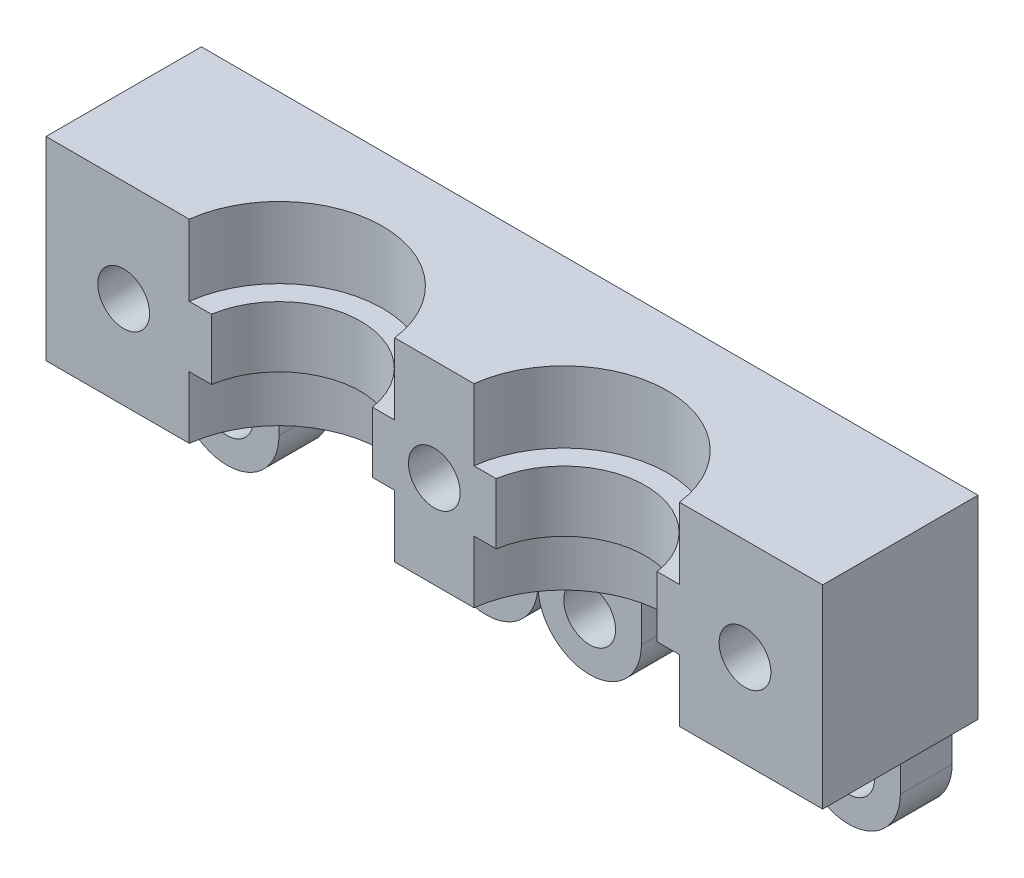
SolidWorks part; units mm, degrees
ref_plane "Piano frontale" through (0, 0, 0) normal (0, 0, 1) x (1, 0, 0)
ref_plane "Piano superiore" through (0, 0, 0) normal (0, 1, 0) x (1, 0, 0)
ref_plane "Piano destro" through (0, 0, 0) normal (1, 0, 0) x (0, 0, -1)
sketch "Schizzo1" plane through (0, 0, 0) normal (0, 0, 1) x (1, 0, 0)
  line L1 (-30, 15) -> (30, 15)
  line L2 (-30, 15) -> (-30, -15)
  line L3 (-30, -15) -> (30, -15)
  line L4 (30, 15) -> (30, -15)
  line L5 (-30, 15) -> (30, -15) construction
  line L6 (-30, -15) -> (30, 15) construction
  point P0 (0, 0)
  dimension "D1" = 60
  dimension "D2" = 30
extrude "Estrusione-Estrusione1" add sketch "Schizzo1" along normal blind 5
sketch "Schizzo2" plane through (0, 0, 5) normal (0, 0, 1) x (1, 0, 0)
  line L0 (-32.3459, -15) -> (49.5432, -15) construction
  line L1 (-32.3459, -8) -> (49.5432, -8) construction
  line L3 (30, -15) -> (30, 15) construction
  line L4 (-30, 15) -> (30, 15)
  line L5 (-30, 15) -> (-30, 7)
  line L6 (-30, 7) -> (30, 7)
  line L7 (30, 15) -> (30, 7)
  dimension "D1" = 7
extrude "Estrusione-Estrusione2" add sketch "Schizzo2" along normal blind 20
sketch "Schizzo3" plane through (0, 15, 0) normal (0, 1, 0) x (1, 0, 0)
  line L0 (0, 7.3603) -> (0, -33.3603) construction
  line L1 (11, 7.3603) -> (11, -33.3603) construction
  line L2 (30, 0) -> (-30, 0) construction
  circle A0 centre (11, -13) radius 5
  circle A1 centre (-11, -13) radius 5
  dimension "D2" = 10
  dimension "D3" = 13
  dimension "D1" = 11
extrude "Taglio-Estrusione1" cut sketch "Schizzo3" against normal up to surface (8 mm away) up to face at (-7.5, 7, 20)
fillet "Raccordo1" radius 20 2 edges at (30, 11, 25) (-30, 11, 25)
sketch "Schizzo4" plane through (0, 0, 5) normal (0, 0, 1) x (1, 0, 0)
  line L0 (-30, 7) -> (30, 7) construction
  line L1 (-30, 7) -> (30, 7)
  line L2 (-30, -8) -> (30, -8)
  line L3 (-30, -8) -> (-30, 7)
  line L4 (30, -8) -> (30, 7)
  dimension "D1" = 15
extrude "Estrusione-Estrusione3" add sketch "Schizzo4" along normal blind 10
sketch "Schizzo6" plane through (0, -8, 0) normal (0, -1, 0) x (1, 0, 0)
  line L0 (0, 28.7661) -> (0, -12.0233) construction
  line L1 (0, -7.3603) -> (0, 33.3603) construction
  circle A0 centre (-11, 13) radius 8
  circle A1 centre (11, 13) radius 8
  dimension "D1" = 16
extrude "Taglio-Estrusione2" cut sketch "Schizzo6" against normal blind 15
ref_plane "Piano1" through (-30, 7, 15) normal (0, -1, 0) x (-1, 0, 0)
sketch "Schizzo8" plane through (0, 0, 15) normal (0, 0, 1) x (1, 0, 0)
  line L1 (-30, 1.5) -> (-30, -3.2)
  line L3 (30, 1.5) -> (30, -3.2)
  line L4 (-30, 1.5) -> (30, 1.5)
  line L5 (-30, -3.2) -> (30, -3.2)
  line L8 (-31.6659, 1.5) -> (35.7067, 1.5) construction
  line L9 (-31.6659, -3.2) -> (35.7067, -3.2) construction
  dimension "D3" = 4.7
extrude "Estrusione-Estrusione4" add sketch "Schizzo8" against normal up to surface (10 mm away) up to face at (0, -10.3333, 5)
sketch "Schizzo9" plane through (0, -3.2, 0) normal (0, -1, 0) x (1, 0, 0)
  line L0 (0, 27.458) -> (0, -16.0891) construction
  line L1 (0, -7.3603) -> (0, 33.3603) construction
  circle A0 centre (-11, 13) radius 6.3
  circle A1 centre (11, 13) radius 6.3
extrude "Taglio-Estrusione3" cut sketch "Schizzo9" against normal blind 5
sketch "Schizzo10" plane through (0, 0, 15) normal (0, 0, 1) x (1, 0, 0)
  line L0 (-31.0418, -0.85) -> (32.2221, -0.85) construction
  circle A0 centre (0, -0.85) radius 2
  circle A1 centre (24, -0.85) radius 2
  circle A2 centre (-24, -0.85) radius 2
extrude "Taglio-Estrusione4" cut sketch "Schizzo10" against normal through all
sketch "Schizzo11" plane through (0, 0, 0) normal (0, 0, -1) x (-1, 0, 0)
  line L1 (-30, 15) -> (30, 15)
  line L2 (-30, 15) -> (-30, 7)
  line L3 (-30, 7) -> (30, 7)
  line L4 (30, 15) -> (30, 7)
extrude "Taglio-Estrusione5" cut sketch "Schizzo11" against normal blind 25
sketch "Schizzo14" plane through (0, -15, 0) normal (0, -1, 0) x (1, 0, 0)
  line L1 (-30, 0) -> (30, 0)
  line L2 (-30, 0) -> (-30, 5)
  line L3 (-30, 5) -> (30, 5)
  line L4 (30, 0) -> (30, 5)
extrude "Taglio-Estrusione7" cut sketch "Schizzo14" against normal up to surface (7 mm away) up to face at (0, -8, 9.0505)
sketch "Schizzo12" plane through (0, 0, 0) normal (0, 0, 1) x (1, 0, 0)
  line L21 (-28, -12.0064) -> (-28, -5.2564)
  line L22 (28, -12.0064) -> (28, -5.2564)
  line L23 (8, -8.0064) -> (20, -8.0064)
  line L24 (20, -12.0064) -> (20, -8.0064)
  line L25 (8, -12.0064) -> (8, -8.0064)
  line L26 (-8, -12.0064) -> (-8, -8.0064)
  line L27 (-20, -12.0064) -> (-20, -8.0064)
  line L28 (-20, -8.0064) -> (-8, -8.0064)
  line L29 (-28, -5.2564) -> (28, -5.2564)
  arc A8 (20, -12.0064) -> (28, -12.0064) centre (24, -12.0064) ccw
  arc A9 (8, -12.0064) -> (0, -12.0064) centre (4, -12.0064) cw
  arc A10 (0, -12.0064) -> (-8, -12.0064) centre (-4, -12.0064) cw
  arc A11 (-20, -12.0064) -> (-28, -12.0064) centre (-24, -12.0064) cw
  circle A12 centre (24, -12.0064) radius 2
  circle A13 centre (-24, -12.0064) radius 2
  circle A14 centre (4, -12.0064) radius 2
  circle A15 centre (-4, -12.0064) radius 2
  point P3 (-59.4844, 2.75)
  point P4 (-3.4844, 2.75)
extrude "Estrusione-Estrusione5" add sketch "Schizzo12" along normal blind 4
sketch "Schizzo17" plane through (0, 0, 15) normal (0, 0, 1) x (1, 0, 0)
  line L1 (30, 7) -> (-30, 7)
  line L2 (30, 7) -> (30, -8)
  line L3 (30, -8) -> (-30, -8)
  line L4 (-30, 7) -> (-30, -8)
extrude "Taglio-Estrusione9" cut sketch "Schizzo17" against normal blind 3
